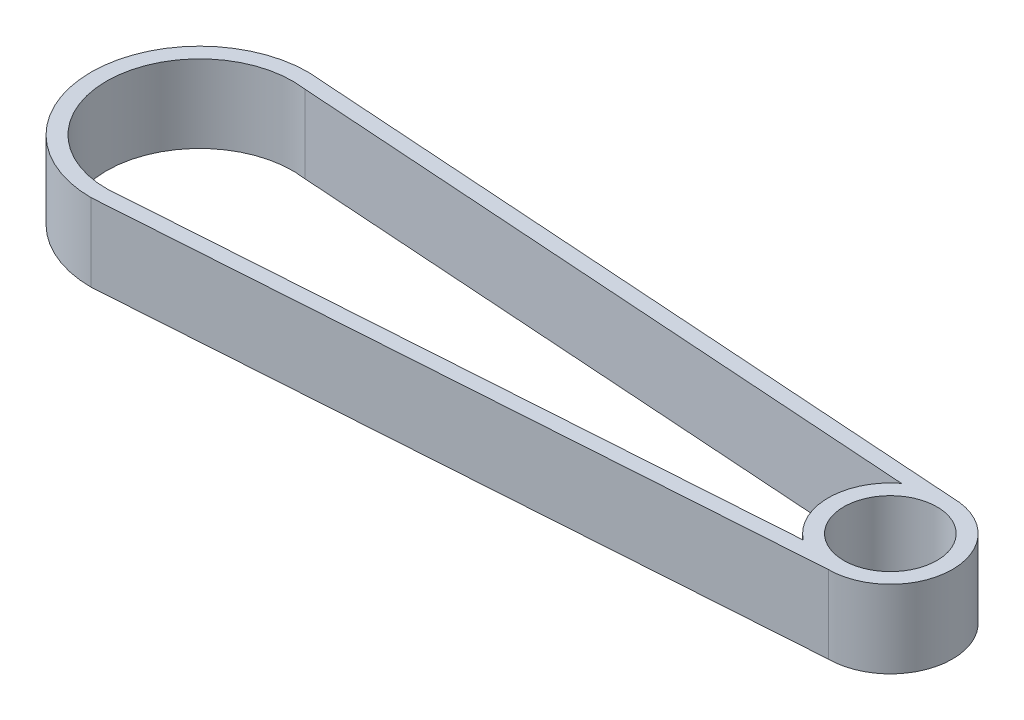
SolidWorks part; units mm, degrees
ref_plane "Front Plane" through (0, 0, 0) normal (0, 0, 1) x (1, 0, 0)
ref_plane "Top Plane" through (0, 0, 0) normal (0, 1, 0) x (1, 0, 0)
ref_plane "Right Plane" through (0, 0, 0) normal (1, 0, 0) x (0, 0, -1)
sketch "Sketch1" plane through (0, 0, 0) normal (0, 1, 0) x (1, 0, 0)
  line L0 (0, 14) -> (89, 8)
  line L1 (0, -14) -> (89, -8)
  line L4 (-0.1345, 12.0045) -> (88.8655, 6.0045)
  line L5 (-0.1345, -12.0045) -> (88.8655, -6.0045)
  line L6 (0, 14) -> (0, -14)
  line L7 (89, 8) -> (89, -8)
  circle A0 centre (0, 0) radius 14
  circle A1 centre (89, 0) radius 8
  circle A2 centre (0, 0) radius 12
  circle A3 centre (89, 0) radius 6
  dimension "D1" = 28
  dimension "D2" = 16
  dimension "D3" = 89
  dimension "D4" = 2
  dimension "D5" = 2
  dimension "D6" = 2
extrude "Boss-Extrude1" add sketch "Sketch1" along normal blind 10
